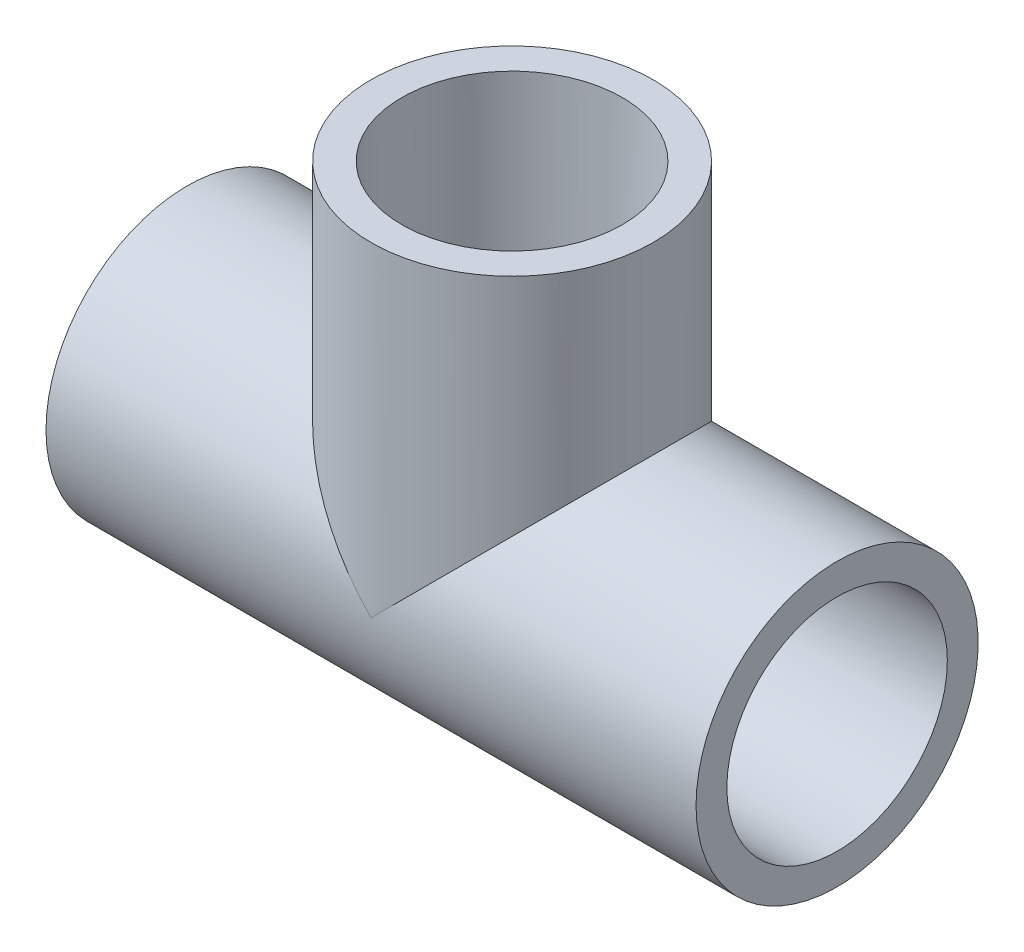
SolidWorks part; units mm, degrees
ref_plane "Front Plane" through (0, 0, 0) normal (0, 0, 1) x (1, 0, 0)
ref_plane "Top Plane" through (0, 0, 0) normal (0, 1, 0) x (1, 0, 0)
ref_plane "Right Plane" through (0, 0, 0) normal (1, 0, 0) x (0, 0, -1)
sketch "Sketch0" plane through (0, 0, 0) normal (0, 0, 1) x (1, 0, 0)
  line L0 (-31.75, 0) -> (0, 0) construction
  line L1 (0, 0) -> (0, 31.75) construction
  line L2 (-12.7, 0) -> (0, 0) construction
  line L3 (0, 0) -> (0, 12.7) construction
  line L4 (-31.75, 13.7795) -> (-31.75, -13.7795) construction
  line L5 (-12.7, 10.6172) -> (-31.75, 10.7696) construction
  line L6 (-12.7, 10.6172) -> (-12.7, -10.6172) construction
  line L7 (-12.7, -10.6172) -> (-31.75, -10.7696) construction
  line L8 (-31.75, 10.7696) -> (-31.75, -10.7696) construction
  line L9 (-13.7795, 31.75) -> (13.7795, 31.75) construction
  line L10 (-10.7696, 31.75) -> (10.7696, 31.75) construction
  line L11 (10.7696, 31.75) -> (10.6172, 12.7) construction
  line L12 (10.6172, 12.7) -> (-10.6172, 12.7) construction
  line L13 (-10.6172, 12.7) -> (-10.7696, 31.75) construction
  line L14 (-12.7, 7.8994) -> (-12.7, -7.8994) construction
  line L15 (-31.75, 0) -> (-12.7, 0) construction
  line L16 (0, 31.75) -> (0, 12.7) construction
  line L17 (0, 0) -> (12.7, 0) construction
  line L18 (-7.8994, 12.7) -> (7.8994, 12.7) construction
  line L19 (12.7, 0) -> (31.75, 0) construction
  dimension "H" = 31.75
  dimension "G" = 12.7
  dimension "M" = 27.559
  dimension "OD A" = 21.5392
  dimension "OD B" = 21.2344
  dimension "ID" = 15.7988
  dimension "H3" = 31.75
sketch "Sketch1" plane through (0, 0, 0) normal (0, 0, 1) x (1, 0, 0)
  line L0 (-31.75, 0) -> (0, 0) construction
  line L1 (-31.75, 0) -> (0, 0) construction
  line L2 (0, 0) -> (0, -13.7795) construction
  line L3 (-31.75, -13.7795) -> (-12.7, -13.7795)
  line L4 (-31.75, -13.7795) -> (-31.75, -10.7696)
  line L5 (-31.75, -10.7696) -> (-12.7, -10.6172)
  line L6 (-12.7, -13.7795) -> (-12.7, -10.6172)
  line L7 (-12.7, -13.7795) -> (0, -13.7795) construction
  line L8 (31.75, -10.7696) -> (12.7, -10.6172)
  line L9 (31.75, -13.7795) -> (31.75, -10.7696)
  line L10 (12.7, -13.7795) -> (12.7, -10.6172)
  line L11 (31.75, -13.7795) -> (12.7, -13.7795)
revolve "Revolve1" add sketch "Sketch1" angle 360 about L1
sketch "Sketch2" plane through (0, 0, 0) normal (0, 0, 1) x (1, 0, 0)
  line L0 (10.7696, 31.75) -> (10.6172, 12.7)
  line L1 (10.6172, 12.7) -> (13.7795, 12.7)
  line L2 (13.7795, 12.7) -> (13.7795, 31.75)
  line L3 (13.7795, 31.75) -> (10.7696, 31.75)
  line L4 (0, 0) -> (0, 31.75) construction
  line L5 (0, 0) -> (0, 31.75) construction
revolve "Revolve2" add sketch "Sketch2" angle 360 about L5
sketch "Sketch3" plane through (-12.7, 0, 0) normal (1, 0, 0) x (0, 0, -1)
  circle A0 centre (0, 0) radius 7.8994
  circle A1 centre (0, 0) radius 13.7795
sketch "Sketch4" plane through (-12.7, 0, 0) normal (1, 0, 0) x (0, 0, -1)
  circle A0 centre (0, 0) radius 13.7795 construction
  circle A1 centre (0, 0) radius 13.7795
extrude "Boss-Extrude1" add sketch "Sketch4" along normal up to vertex
sketch "Sketch5" plane through (0, 12.7, 0) normal (0, -1, 0) x (1, 0, 0)
  circle A0 centre (0, 0) radius 13.7795 construction
  circle A1 centre (0, 0) radius 13.7795
extrude "Boss-Extrude2" add sketch "Sketch5" along normal up to vertex (12.7 mm away) up to point (0, 0, 0)
sketch "Sketch6" plane through (0, 0, 0) normal (0, 0, 1) x (1, 0, 0)
  line L0 (-31.75, -10.7696) -> (-12.7, -10.6172)
  line L1 (-12.7, -10.6172) -> (-12.7, -7.8994)
  line L2 (-12.7, -7.8994) -> (12.7, -7.8994)
  line L3 (12.7, -10.6172) -> (12.7, 9.1728) construction
  line L4 (0, -7.8994) -> (0, 0) construction
  line L5 (12.7, -10.6172) -> (12.7, -7.8994)
  line L6 (31.75, -10.7696) -> (31.75, 10.7696) construction
  line L7 (31.75, -13.7795) -> (31.75, 13.7795) construction
  line L8 (31.75, -10.7696) -> (31.75, 0)
  line L9 (31.75, 0) -> (-31.75, 0)
  line L10 (-31.75, 0) -> (-31.75, -10.7696)
  line L11 (31.75, -10.7696) -> (12.7, -10.6172)
revolve "Cut-Revolve1" cut sketch "Sketch6" angle 360 about L9
sketch "Sketch7" plane through (0, 0, 0) normal (0, 0, 1) x (1, 0, 0)
  line L0 (10.7696, 31.75) -> (10.6172, 12.7)
  line L1 (10.6172, 12.7) -> (7.8994, 12.7)
  line L2 (7.8994, 12.7) -> (7.8994, 0)
  line L3 (0, 0) -> (12.7, 0) construction
  line L4 (7.8994, 0) -> (0, 0)
  line L5 (0, 0) -> (0, 31.75)
  line L6 (-13.7795, 31.75) -> (13.7795, 31.75) construction
  line L7 (0, 31.75) -> (10.7696, 31.75)
revolve "Cut-Revolve2" cut sketch "Sketch7" angle 360 about L5
hole_wizard "3/8 (0.375) Diameter Hole1" positions "Sketch9" profile "Sketch8" hole size "3/8" standard "ANSI Inch" end condition through all
sketch "Sketch9" plane through (0, 31.75, 0) normal (0, 1, 0) x (-1, 0, 0)
  point P0 (0, 0)
sketch "Sketch8" plane through (0, 31.75, 0) normal (1, 0, 0) x (0, 0, 1)
  line L0 (0, 0) -> (0, 45.5295)
  line L1 (0, 45.5295) -> (4.7625, 45.5295)
  line L2 (4.7625, 45.5295) -> (4.7625, 0)
  line L5 (4.7625, 0) -> (0, 0)
  line L11 (0, -6.35) -> (0, 107.95) construction
  dimension "Thru Hole Dia." = 9.525
  dimension "Thru Hole Depth" = 45.5295
